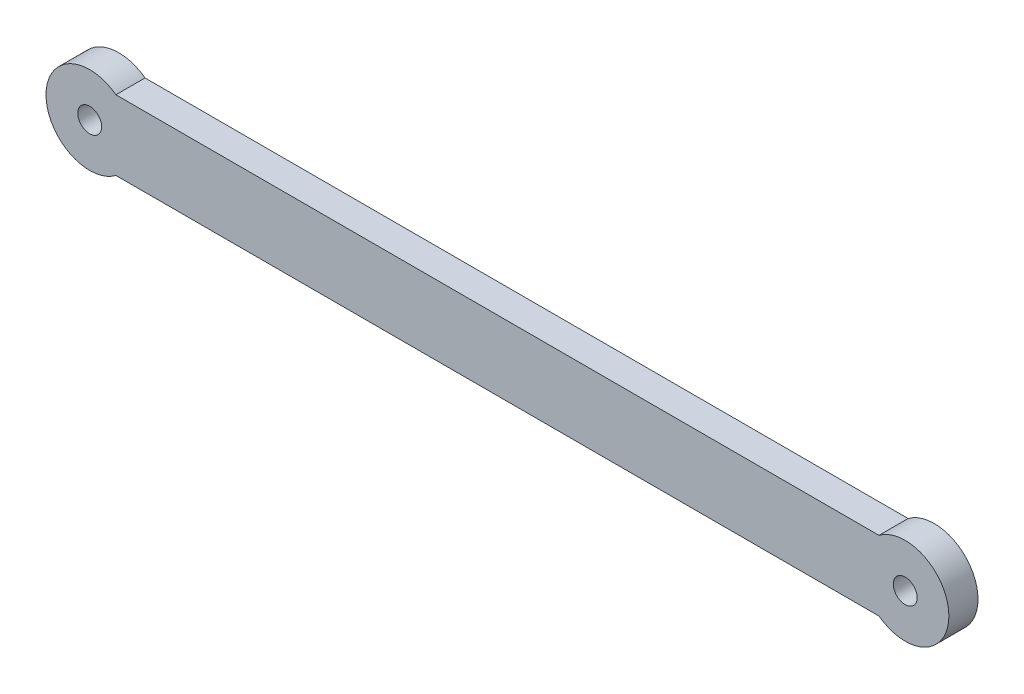
SolidWorks part; units mm, degrees
material "Acrílico (Impacto medio-alto)"
ref_plane "Piano frontale" through (0, 0, 0) normal (0, 0, 1) x (1, 0, 0)
ref_plane "Piano superiore" through (0, 0, 0) normal (0, 1, 0) x (1, 0, 0)
ref_plane "Piano destro" through (0, 0, 0) normal (1, 0, 0) x (0, 0, -1)
sketch "Schizzo1" plane through (0, 0, 0) normal (0, 0, 1) x (1, 0, 0)
  line L0 (0, 0) -> (2.05, 0) construction
  line L1 (4.5, -6) -> (135.5, -6)
  line L2 (4.5, 6) -> (135.5, 6)
  line L3 (0, 6) -> (140, 6) construction
  line L4 (0, -6) -> (140, -6) construction
  line L5 (137.95, 0) -> (140, 0) construction
  line L6 (0, 0) -> (140, 0) construction
  circle A0 centre (0, 0) radius 2.05
  circle A1 centre (140, 0) radius 2.05
  arc A2 (4.5, 6) -> (4.5, -6) centre (0, 0) ccw
  arc A3 (135.5, -6) -> (135.5, 6) centre (140, 0) ccw
  dimension "D1" = 4.1
  dimension "D4" = 15
  dimension "D5" = 15
  dimension "D3" = 140
  dimension "D6" = 6
  dimension "D7" = 6
extrude "Estrusione-Estrusione1" add sketch "Schizzo1" along normal blind 5
